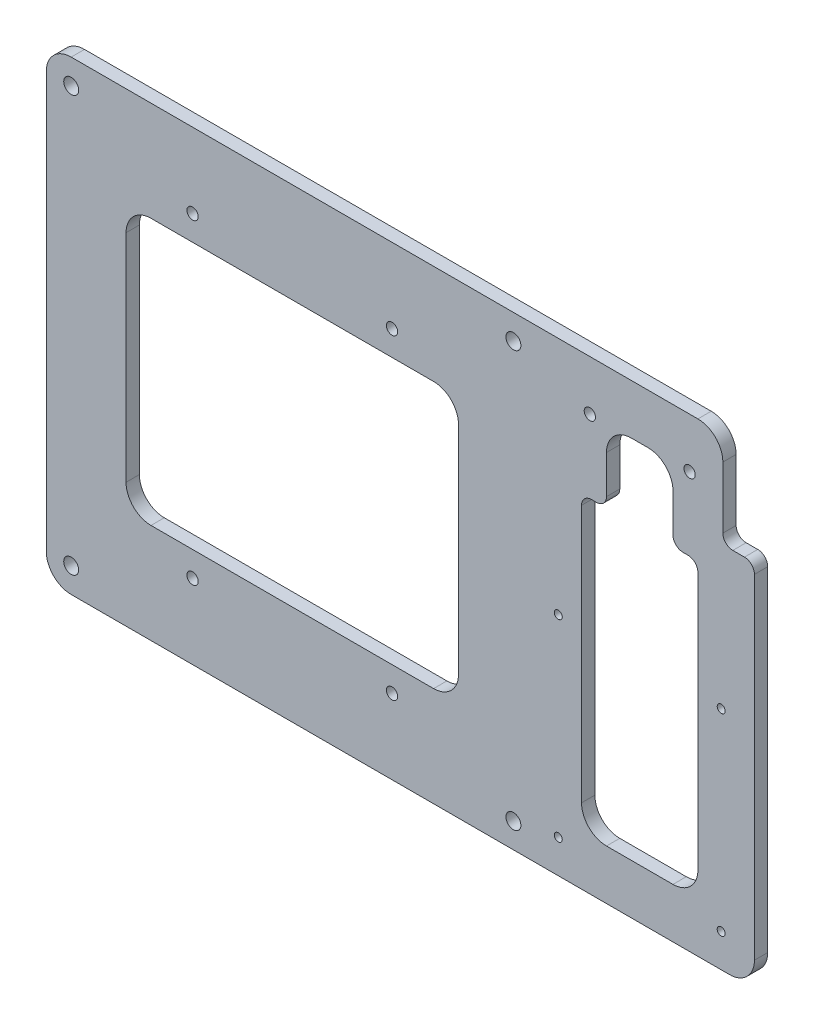
SolidWorks part; units mm, degrees
material "MDF"
ref_plane "正面" through (0, 0, 0) normal (1, 0, 0) x (0, 1, 0)
ref_plane "平面" through (0, 0, 0) normal (0, 0, 1) x (0, 1, 0)
ref_plane "右側面" through (0, 0, 0) normal (0, 1, 0) x (-1, 0, 0)
sketch "ｽｹｯﾁ1" plane through (0, 0, 0) normal (0, 0, 1) x (0, 1, 0)
  line L1 (0, 0) -> (140, 0)
  line L2 (0, 0) -> (0, -148)
  line L3 (0, -148) -> (140, -148)
  line L4 (140, 0) -> (140, -148)
  line L5 (70, -148) -> (70, 0) construction
  line L6 (0, -74) -> (140, -74) construction
  line L7 (110, -124) -> (30, -124)
  line L9 (110, -24) -> (30, -24)
  line L10 (30, -124) -> (30, -74)
  line L11 (110, -124) -> (30, -24) construction
  line L12 (110, -24) -> (30, -124) construction
  line L15 (30, -74) -> (30, -24)
  line L16 (110, -124) -> (110, -24)
  point P4 (70, -74)
  point P13 (0, 0)
  point P512 (70, -74)
  dimension "D1" = 148
  dimension "D2" = 140
  dimension "D3" = 80
  dimension "D4" = 100
extrude "ﾎﾞｽ - 押し出し1" add sketch "ｽｹｯﾁ1" along normal blind 4
sketch "ｽｹｯﾁ2" plane through (0, 0, 4) normal (0, 0, 1) x (1, 0, 0)
  line L0 (0, 0) -> (148, 0) construction
  line L1 (148, 140) -> (0, 140) construction
  point P0 (7.5, 132.5)
  point P1 (140.5, 132.5)
  point P2 (7.5, 7.5)
  point P3 (140.5, 7.5)
  point P10 (74, 140)
  dimension "D1" = 7.5
  dimension "D2" = 7.5
  dimension "D3" = 133
  dimension "D5" = 66.5
hole_wizard "M4 すきま穴1" positions "ｽｹｯﾁ2" profile "ｽｹｯﾁ3" hole size "M4" standard "JIS" end condition through all
sketch "ｽｹｯﾁ3" plane through (7.5, 132.5, 4) normal (1, 0, 0) x (0, -1, 0)
  line L0 (0, 0) -> (0, 4)
  line L1 (0, 4) -> (2.25, 4)
  line L2 (2.25, 4) -> (2.25, 0)
  line L5 (2.25, 0) -> (0, 0)
  line L11 (0, -6.35) -> (0, 107.95) construction
  dimension "通し穴の直径" = 4.5
  dimension "通し穴の深さ" = 4
sketch "ｽｹｯﾁ4" plane through (0, 0, 4) normal (0, 0, 1) x (1, 0, 0)
  line L0 (148, 140) -> (0, 140) construction
  line L1 (148, 0) -> (148, 140) construction
  line L2 (148, 70) -> (0, 70) construction
  line L3 (0, 140) -> (0, 0) construction
  point P0 (44, 117.5)
  point P1 (104, 117.5)
  point P4 (74, 140)
  point P7 (148, 70)
  point P8 (104, 22.5)
  point P13 (44, 22.5)
  dimension "D1" = 60
  dimension "D2" = 30
  dimension "D3" = 47.5
hole_wizard "M3 すきま穴2" positions "ｽｹｯﾁ4" profile "ｽｹｯﾁ5" hole size "M3" standard "JIS" end condition through all
sketch "ｽｹｯﾁ5" plane through (44, 117.5, 4) normal (1, 0, 0) x (0, -1, 0)
  line L0 (0, 0) -> (0, 4)
  line L1 (0, 4) -> (1.7, 4)
  line L2 (1.7, 4) -> (1.7, 0)
  line L5 (1.7, 0) -> (0, 0)
  line L11 (0, -6.35) -> (0, 107.95) construction
  dimension "通し穴の直径" = 3.4
  dimension "通し穴の深さ" = 4
sketch "ｽｹｯﾁ9" plane through (0, 0, 4) normal (0, 0, 1) x (1, 0, 0)
  line L0 (148, 140) -> (0, 140) construction
  line L7 (148, 0) -> (213, 0)
  line L8 (148, 0) -> (148, 140)
  line L9 (148, 140) -> (213, 140)
  line L10 (213, 0) -> (213, 140)
  line L11 (148, 0) -> (213, 140) construction
  line L12 (148, 140) -> (213, 0) construction
  point P10 (180.5, 70)
  dimension "D3" = 65
extrude "ﾎﾞｽ - 押し出し3" add sketch "ｽｹｯﾁ9" against normal blind 4
sketch "ｽｹｯﾁ11" plane through (0, 0, 4) normal (0, 0, 1) x (1, 0, 0)
  line L0 (213, 0) -> (213, 140) construction
  line L1 (0, 0) -> (213, 0) construction
  point P0 (203, 10)
  point P1 (154, 68)
  point P7 (203, 68)
  point P9 (154, 10)
  point P10 (0, 0)
  point P11 (0, 0)
  point P12 (0, 0)
  point P13 (0, 0)
  dimension "D1" = 49
  dimension "D2" = 58
  dimension "D3" = 10
  dimension "D4" = 10
hole_wizard "M2 すきま穴1" positions "ｽｹｯﾁ11" profile "ｽｹｯﾁ12" hole size "M2" standard "JIS" end condition through all
sketch "ｽｹｯﾁ12" plane through (203, 10, 4) normal (1, 0, 0) x (0, -1, 0)
  line L0 (0, 0) -> (0, 4)
  line L1 (0, 4) -> (1.2, 4)
  line L2 (1.2, 4) -> (1.2, 0)
  line L5 (1.2, 0) -> (0, 0)
  line L11 (0, -6.35) -> (0, 107.95) construction
  dimension "通し穴の直径" = 2.4
  dimension "通し穴の深さ" = 4
sketch "ｽｹｯﾁ13" plane through (0, 0, 4) normal (0, 0, 1) x (1, 0, 0)
  line L0 (0, 0) -> (213, 0) construction
  line L1 (168.5, 125) -> (188.5, 125)
  line L2 (168.5, 125) -> (168.5, 103)
  line L4 (188.5, 125) -> (188.5, 103)
  line L5 (168.5, 125) -> (188.5, 103) construction
  line L6 (168.5, 103) -> (188.5, 125) construction
  line L7 (154, 68) -> (203, 68) construction
  line L8 (154, 68) -> (154, 10) construction
  line L9 (154, 10) -> (203, 10) construction
  line L10 (203, 68) -> (203, 10) construction
  line L11 (161, 103) -> (168.5, 103)
  line L12 (161, 103) -> (161, 15)
  line L13 (161, 15) -> (196, 15)
  line L14 (196, 103) -> (196, 15)
  line L15 (213, 140) -> (0, 140) construction
  line L16 (188.5, 103) -> (196, 103)
  line L18 (213, 140) -> (203.5, 140)
  line L19 (213, 140) -> (213, 111)
  line L20 (213, 111) -> (203.5, 111)
  line L21 (203.5, 140) -> (203.5, 111)
  point P4 (178.5, 114)
  point P11 (178.5, 68)
  point P21 (178.5, 15)
  point P22 (192.25, 103)
  dimension "D1" = 20
  dimension "D2" = 15
  dimension "D3" = 35
  dimension "D4" = 15
  dimension "D5" = 35
  dimension "D6" = 15
  dimension "D7" = 8
extrude "ｶｯﾄ - 押し出し1" cut sketch "ｽｹｯﾁ13" against normal through all
sketch "ｽｹｯﾁ14" plane through (0, 0, 4) normal (0, 0, 1) x (1, 0, 0)
  line L0 (168.5, 125) -> (168.5, 103) construction
  line L1 (188.5, 103) -> (188.5, 125) construction
  line L2 (203.5, 140) -> (0, 140) construction
  point P0 (163.5, 125)
  point P1 (193.5, 125)
  point P7 (163.5, 124.0448)
  dimension "D1" = 5
  dimension "D2" = 5
  dimension "D3" = 15
hole_wizard "M3 すきま穴1" positions "ｽｹｯﾁ14" profile "ｽｹｯﾁ15" hole size "M3" standard "JIS" end condition through all
sketch "ｽｹｯﾁ15" plane through (163.5, 125, 4) normal (1, 0, 0) x (0, -1, 0)
  line L0 (0, 0) -> (0, 4)
  line L1 (0, 4) -> (1.7, 4)
  line L2 (1.7, 4) -> (1.7, 0)
  line L5 (1.7, 0) -> (0, 0)
  line L11 (0, -6.35) -> (0, 107.95) construction
  dimension "通し穴の直径" = 3.4
  dimension "通し穴の深さ" = 4
fillet "ﾌｨﾚｯﾄ12" radius 7.5 12 edges at (24, 30, 2) (124, 30, 2) (0, 140, 2) (0, 0, 2) (24, 110, 2) (213, 0, 2) (168.5, 125, 2) (188.5, 125, 2) (196, 15, 2) (161, 15, 2) (124, 110, 2) (203.5, 140, 2)
fillet "ﾌｨﾚｯﾄ11" radius 3 6 edges at (188.5, 103, 2) (161, 103, 2) (168.5, 103, 2) (196, 103, 2) (203.5, 111, 2) (213, 111, 2)
equation "\"D1@ｽｹｯﾁ2\"= \"D2@ｽｹｯﾁ2\""
equation "\"D5@ｽｹｯﾁ2\"= \"D3@ｽｹｯﾁ2\" / 2"
